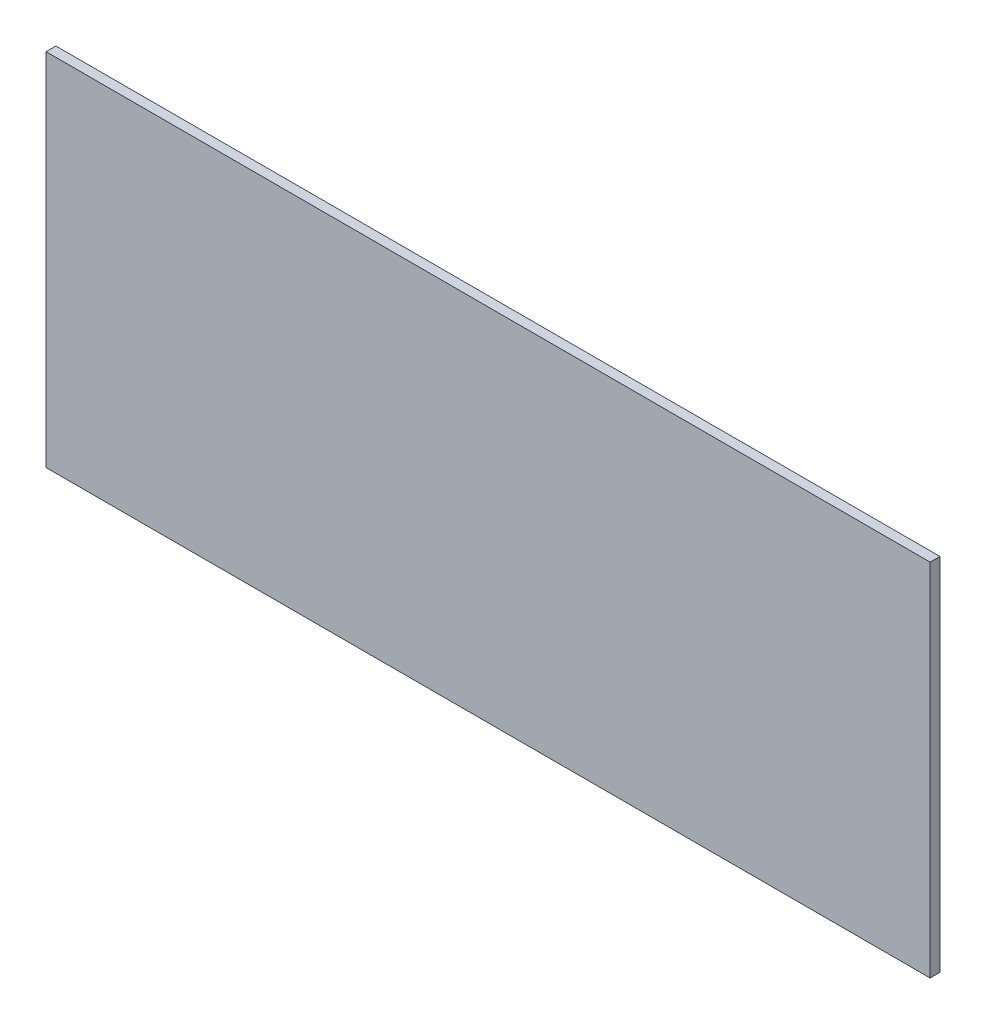
SolidWorks part; units mm, degrees
material "Birch plywood FK"
ref_plane "Спереди" through (0, 0, 0) normal (0, 0, 1) x (1, 0, 0)
ref_plane "Сверху" through (0, 0, 0) normal (0, 1, 0) x (1, 0, 0)
ref_plane "Справа" through (0, 0, 0) normal (1, 0, 0) x (0, 0, -1)
sketch "Эскиз1" plane through (0, 0, 0) normal (0, 0, 1) x (1, 0, 0)
  line L1 (270, -110) -> (-270, -110)
  line L2 (270, -110) -> (270, 110)
  line L3 (270, 110) -> (-270, 110)
  line L4 (-270, -110) -> (-270, 110)
  line L5 (270, -110) -> (-270, 110) construction
  line L6 (270, 110) -> (-270, -110) construction
  point P0 (0, 0)
  dimension "D1" = 540
  dimension "D2" = 220
extrude "Бобышка-Вытянуть1" add sketch "Эскиз1" along normal blind 6
